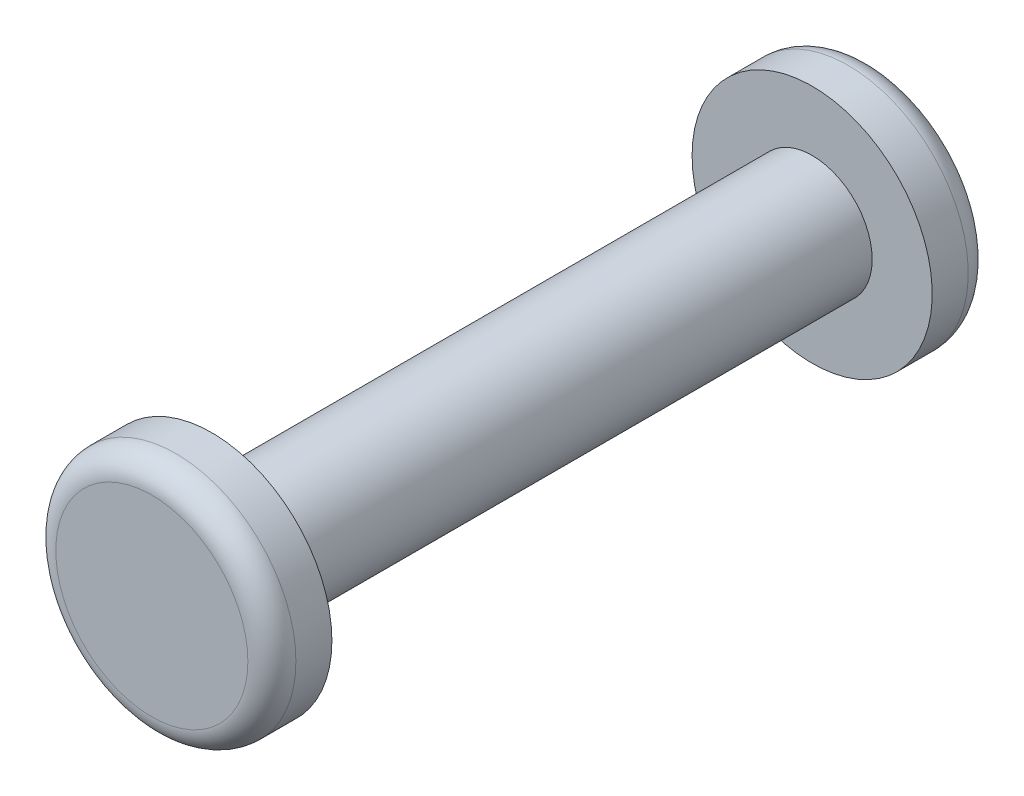
SolidWorks part; units mm, degrees
ref_plane "Front Plane" through (0, 0, 0) normal (0, 0, 1) x (1, 0, 0)
ref_plane "Top Plane" through (0, 0, 0) normal (0, 1, 0) x (1, 0, 0)
ref_plane "Right Plane" through (0, 0, 0) normal (1, 0, 0) x (0, 0, -1)
sketch "Sketch1" plane through (0, 0, 0) normal (0, 0, 1) x (1, 0, 0)
  circle A0 centre (0, 0) radius 5
  dimension "D1" = 10
extrude "Boss-Extrude1" add sketch "Sketch1" along normal mid plane 50
sketch "Sketch2" plane through (0, 0, 25) normal (0, 0, 1) x (1, 0, 0)
  circle A0 centre (0, 0) radius 10
extrude "Boss-Extrude2" add sketch "Sketch2" along normal blind 5
sketch "Sketch3" plane through (0, 0, -25) normal (0, 0, -1) x (-1, 0, 0)
  circle A0 centre (0, 0) radius 10
  dimension "D1" = 20
extrude "Boss-Extrude3" add sketch "Sketch3" along normal blind 5
fillet "Fillet1" radius 2 1 edges at (10, 0, 30)
fillet "Fillet2" radius 2 1 edges at (-10, 0, -30)
